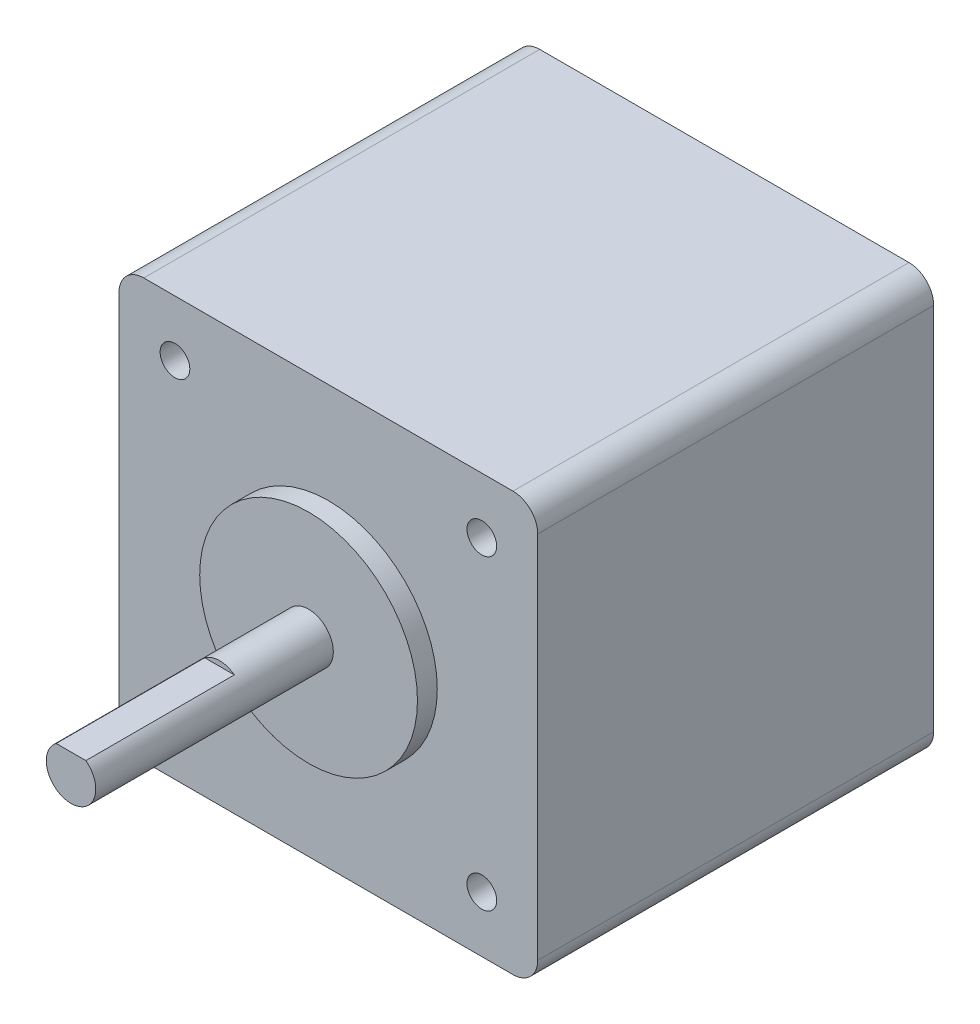
SolidWorks part; units mm, degrees
ref_plane "Plano frontal" through (0, 0, 0) normal (0, 0, 1) x (1, 0, 0)
ref_plane "Plano superior" through (0, 0, 0) normal (0, 1, 0) x (1, 0, 0)
ref_plane "Plano direito" through (0, 0, 0) normal (1, 0, 0) x (0, 0, -1)
sketch "Esboço1" plane through (0, 0, 0) normal (0, 0, 1) x (1, 0, 0)
  line L1 (21.15, -21.15) -> (-21.15, -21.15)
  line L2 (21.15, -21.15) -> (21.15, 21.15)
  line L3 (21.15, 21.15) -> (-21.15, 21.15)
  line L4 (-21.15, -21.15) -> (-21.15, 21.15)
  line L5 (21.15, -21.15) -> (-21.15, 21.15) construction
  line L6 (21.15, 21.15) -> (-21.15, -21.15) construction
  point P0 (0, 0)
  dimension "D1" = 42.3
  dimension "D2" = 42.3
extrude "Ressalto-extrusão1" add sketch "Esboço1" along normal blind 40
fillet "Filete1" radius 2.5 4 edges at (21.15, -21.15, 20) (-21.15, -21.15, 20) (21.15, 21.15, 20) (-21.15, 21.15, 20)
sketch "Esboço2" plane through (0, 0, 40) normal (0, 0, 1) x (1, 0, 0)
  line L0 (0, -32.3814) -> (0, 33.2669) construction
  line L1 (-36.8049, 0) -> (38.3105, 0) construction
  circle A0 centre (-15.5, 15.5) radius 1.5
  circle A1 centre (15.5, 15.5) radius 1.5
  circle A2 centre (15.5, -15.5) radius 1.5
  circle A3 centre (-15.5, -15.5) radius 1.5
  dimension "D1" = 3
  dimension "D2" = 15.5
  dimension "D3" = 15.5
  dimension "D4" = 4
extrude "Corte-extrusão2" cut sketch "Esboço2" against normal blind 4.5
sketch "Esboço3" plane through (0, 0, 40) normal (0, 0, 1) x (1, 0, 0)
  circle A0 centre (0, 0) radius 11
  dimension "D1" = 22
extrude "Ressalto-extrusão2" add sketch "Esboço3" along normal blind 2
sketch "Esboço4" plane through (0, 0, 42) normal (0, 0, 1) x (1, 0, 0)
  circle A0 centre (0, 0) radius 2.5
  dimension "D1" = 5
extrude "Ressalto-extrusão3" add sketch "Esboço4" along normal blind 24
sketch "Esboço5" plane through (0, 0, 66) normal (0, 0, 1) x (1, 0, 0)
  line L0 (0, -5.6767) -> (0, 6.8493) construction
  line L2 (4, 2) -> (-4, 2)
  line L3 (4, 2) -> (4, 3)
  line L4 (4, 3) -> (-4, 3)
  line L5 (-4, 2) -> (-4, 3)
  line L6 (4, 2) -> (-4, 3) construction
  line L7 (4, 3) -> (-4, 2) construction
  circle A0 centre (0, 0) radius 2.5 construction
  point P3 (0, 2.5)
  dimension "D1" = 1
  dimension "D2" = 8
extrude "Corte-extrusão3" cut sketch "Esboço5" against normal blind 15
